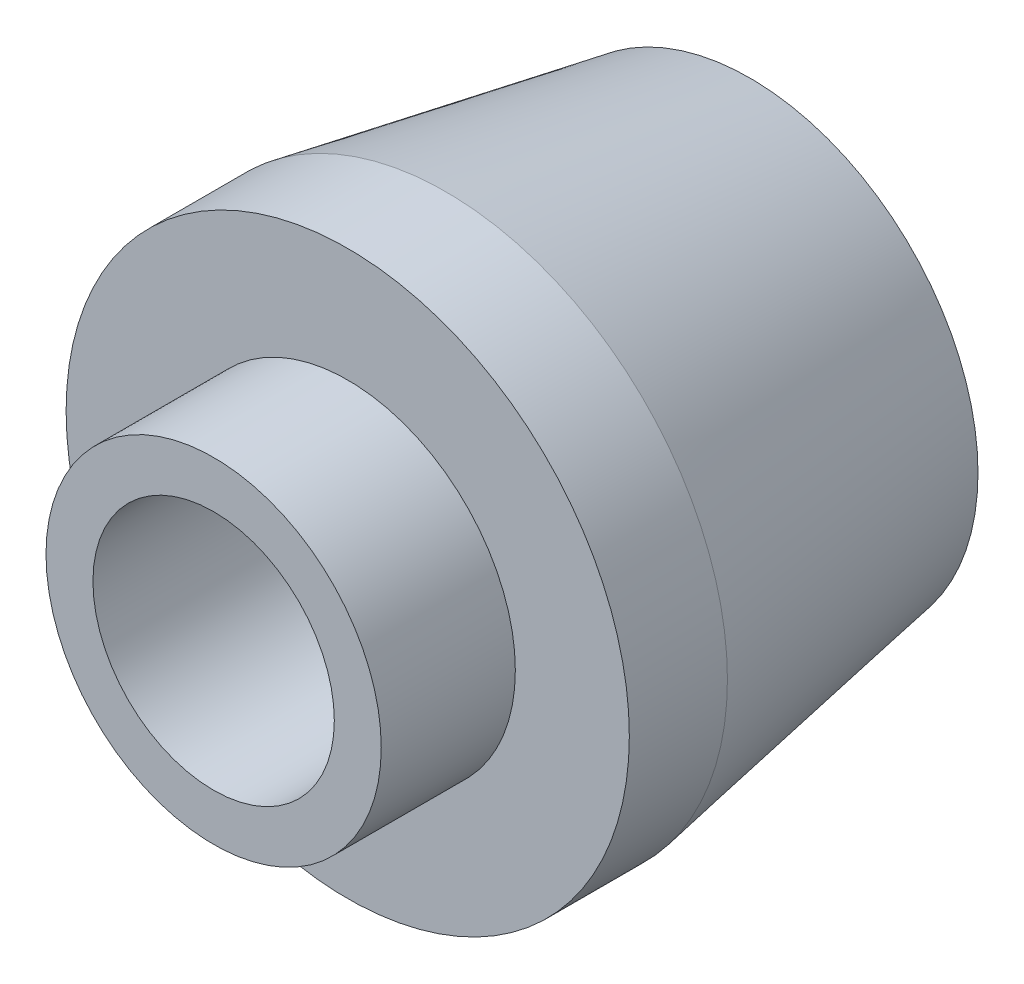
SolidWorks part; units mm, degrees
ref_plane "Front Plane" through (0, 0, 0) normal (0, 0, 1) x (1, 0, 0)
ref_plane "Top Plane" through (0, 0, 0) normal (0, 1, 0) x (1, 0, 0)
ref_plane "Right Plane" through (0, 0, 0) normal (1, 0, 0) x (0, 0, -1)
sketch "Sketch1" plane through (0, 0, 0) normal (0, 0, 1) x (1, 0, 0)
  circle A0 centre (0, 0) radius 10.5
  dimension "D1" = 21
extrude "Boss-Extrude1" add sketch "Sketch1" along normal blind 15
sketch "Sketch2" plane through (0, 0, 15) normal (0, 0, 1) x (1, 0, 0)
  circle A0 centre (0, 0) radius 6.25
  dimension "D1" = 12.5
extrude "Boss-Extrude2" add sketch "Sketch2" along normal blind 5
hole_wizard "M10x1.0 Tapped Hole1" positions "Sketch3" profile "Sketch4" tap size "M10x1.0" standard "ANSI Metric" end condition through all
sketch "Sketch3" plane through (0, 0, 0) normal (0, 0, -1) x (-1, 0, 0)
  point P0 (0, 0)
sketch "Sketch4" plane through (0, 0, 0) normal (1, 0, 0) x (0, 1, 0)
  line L0 (0, 0) -> (0, 20)
  line L1 (0, 20) -> (4.5, 20)
  line L2 (4.5, 20) -> (4.5, 0.525)
  line L3 (4.5, 0.525) -> (5.025, 0)
  line L5 (5.025, 0) -> (0, 0)
  line L6 (-4.5, 0.525) -> (-5.025, 0) construction
  line L11 (0, -6.35) -> (0, 107.95) construction
  dimension "Thru Tap Drill Dia." = 9
  dimension "Thru Tap Drill Depth" = 20
  dimension "Near C'Sink Dia." = 10.05
  dimension "Near C'Sink Angle" = 90
cosmetic thread "Hole Thread1" parameters "D2"=10
chamfer "Chamfer1" distance 2 angle 80 1 edges at (10.5, 0, 0)
